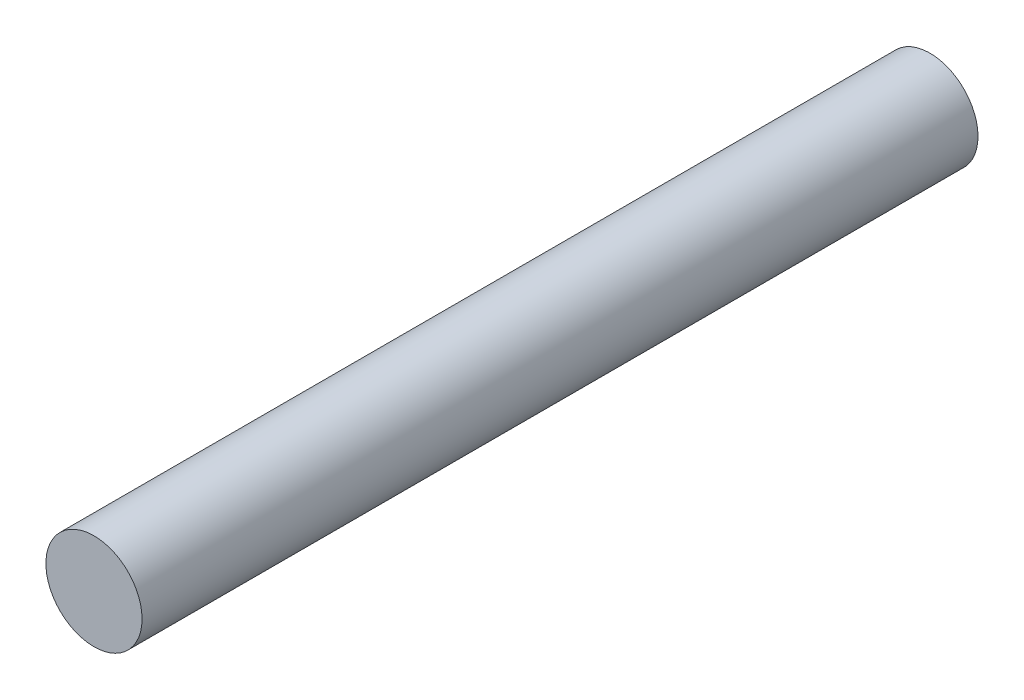
SolidWorks part; units mm, degrees
ref_plane "Front Plane" through (0, 0, 0) normal (0, 0, 1) x (1, 0, 0)
ref_plane "Top Plane" through (0, 0, 0) normal (0, 1, 0) x (1, 0, 0)
ref_plane "Right Plane" through (0, 0, 0) normal (1, 0, 0) x (0, 0, -1)
sketch "Sketch1" plane through (0, 0, 0) normal (0, 0, 1) x (1, 0, 0)
  circle A0 centre (0, 0) radius 5.842
  point P3 (0, 0)
extrude "Boss-Extrude2" add sketch "Sketch1" along normal blind 101.6
